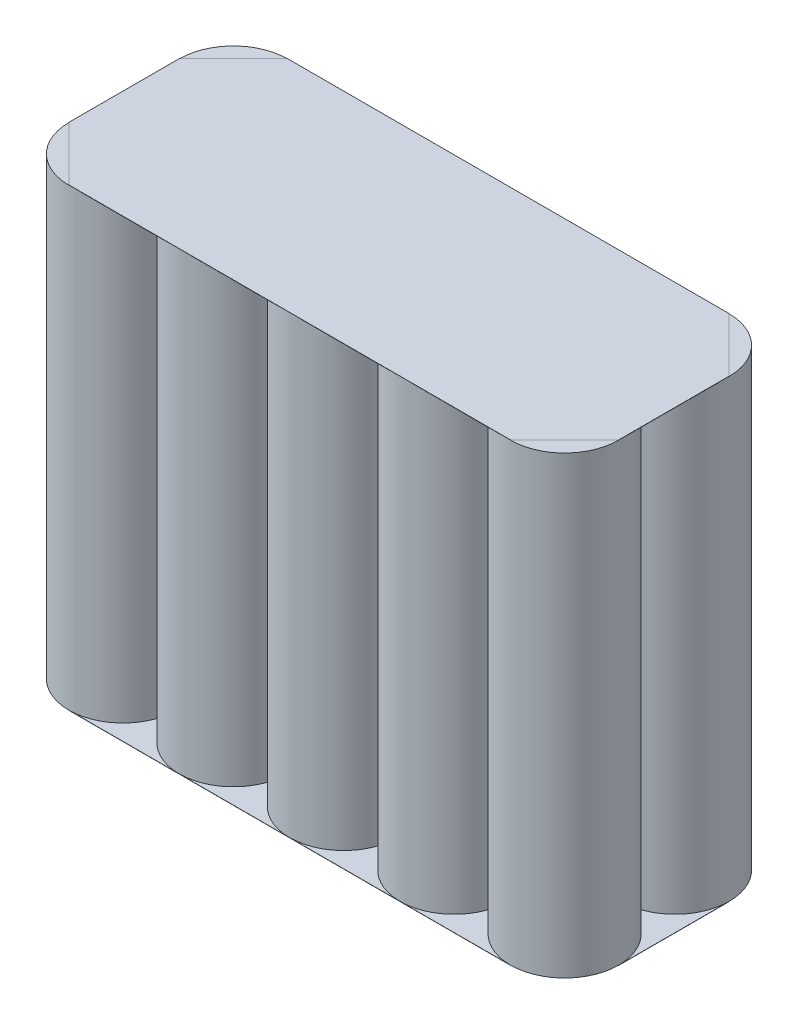
SolidWorks part; units mm, degrees
material "Duranickel(R) 301"
ref_plane "Front Plane" through (0, 0, 0) normal (0, 0, 1) x (1, 0, 0)
ref_plane "Top Plane" through (0, 0, 0) normal (0, 1, 0) x (1, 0, 0)
ref_plane "Right Plane" through (0, 0, 0) normal (1, 0, 0) x (0, 0, -1)
sketch "Sketch1" plane through (0, 0, 0) normal (0, 1, 0) x (1, 0, 0)
  line L0 (0, 0) -> (0, 27.6274) construction
  line L1 (0, 0) -> (33.5964, 0) construction
  circle A0 centre (0, 0) radius 6.35
  circle A1 centre (12.954, 0) radius 6.35
  circle A2 centre (25.908, 0) radius 6.35
  circle A3 centre (38.862, 0) radius 6.35
  circle A4 centre (51.816, 0) radius 6.35
  circle A5 centre (12.954, -12.954) radius 6.35
  circle A6 centre (25.908, -12.954) radius 6.35
  circle A7 centre (38.862, -12.954) radius 6.35
  circle A8 centre (51.816, -12.954) radius 6.35
  circle A9 centre (0, -12.954) radius 6.35
  dimension "D1" = 5
  dimension "D2" = 2
extrude "Boss-Extrude1" add sketch "Sketch1" along normal blind 50.8
ref_plane "Plane1" through (0, 25.4, 0) normal (0, 1, 0) x (1, 0, 0)
sketch "Sketch4" plane through (0, 50.8, 0) normal (0, 1, 0) x (1, 0, 0)
  line L0 (0, -6.604) -> (0, -6.35)
  line L1 (6.35, 0) -> (6.604, 0)
  line L2 (19.304, 0) -> (19.558, 0)
  line L3 (32.258, 0) -> (32.512, 0)
  line L4 (45.212, 0) -> (45.466, 0)
  line L5 (51.816, -6.35) -> (51.816, -6.604)
  line L6 (45.212, -12.954) -> (45.466, -12.954)
  line L7 (32.258, -12.954) -> (32.512, -12.954)
  line L8 (19.304, -12.954) -> (19.558, -12.954)
  line L9 (6.35, -12.954) -> (6.604, -12.954)
  circle A1 centre (38.862, 0) radius 6.35
  arc A2 (45.212, 0) -> (32.512, 0) centre (38.862, 0) ccw
  circle A3 centre (25.908, 0) radius 6.35
  arc A4 (32.258, 0) -> (19.558, 0) centre (25.908, 0) ccw
  circle A5 centre (12.954, 0) radius 6.35
  arc A6 (19.304, 0) -> (6.604, 0) centre (12.954, 0) ccw
  circle A7 centre (0, 0) radius 6.35
  arc A8 (6.35, 0) -> (0, -6.35) centre (0, 0) ccw
  circle A9 centre (0, -12.954) radius 6.35
  arc A10 (0, -6.604) -> (6.35, -12.954) centre (0, -12.954) ccw
  circle A11 centre (51.816, -12.954) radius 6.35
  arc A12 (45.466, -12.954) -> (51.816, -6.604) centre (51.816, -12.954) ccw
  circle A13 centre (38.862, -12.954) radius 6.35
  arc A14 (32.512, -12.954) -> (45.212, -12.954) centre (38.862, -12.954) ccw
  circle A15 centre (25.908, -12.954) radius 6.35
  arc A16 (19.558, -12.954) -> (32.258, -12.954) centre (25.908, -12.954) ccw
  circle A17 centre (12.954, -12.954) radius 6.35
  arc A18 (6.604, -12.954) -> (19.304, -12.954) centre (12.954, -12.954) ccw
  circle A19 centre (51.816, 0) radius 6.35
  arc A20 (51.816, -6.35) -> (45.466, 0) centre (51.816, 0) ccw
  dimension "D1" = 0
  dimension "D2" = 0
  dimension "D3" = 0
  dimension "D4" = 0
  dimension "D5" = 0
  dimension "D6" = 0
  dimension "D7" = 0
  dimension "D8" = 0
  dimension "D9" = 0
  dimension "D10" = 0
extrude "Boss-Extrude2" add sketch "Sketch4" along normal blind 1.27
mirror "Mirror1" about plane through (0, 25.4, 0) normal (0, 1, 0) of "Boss-Extrude2"
sketch "Sketch5" plane through (0, 52.07, 0) normal (0, 1, 0) x (1, 0, 0)
  line L0 (51.816, 6.35) -> (0, 6.35)
  line L1 (0, 6.35) -> (-6.35, 0)
  line L2 (-6.35, 0) -> (-6.35, -12.954)
  line L3 (-6.35, -12.954) -> (0, -19.304)
  line L4 (0, -19.304) -> (51.816, -19.304)
  line L5 (51.816, -19.304) -> (58.166, -12.954)
  line L6 (51.816, 6.35) -> (58.166, 0)
  line L7 (58.166, 0) -> (58.166, -12.954)
  arc A0 (51.816, -6.35) -> (45.466, 0) centre (51.816, 0) ccw construction
  arc A1 (6.35, 0) -> (0, -6.35) centre (0, 0) ccw construction
  arc A2 (0, -6.604) -> (6.35, -12.954) centre (0, -12.954) ccw construction
  arc A3 (45.466, -12.954) -> (51.816, -6.604) centre (51.816, -12.954) ccw construction
extrude "Boss-Extrude3" add sketch "Sketch5" along normal blind 0.0254
mirror "Mirror2" about plane through (0, 25.4, 0) normal (0, 1, 0) of "Boss-Extrude3"
